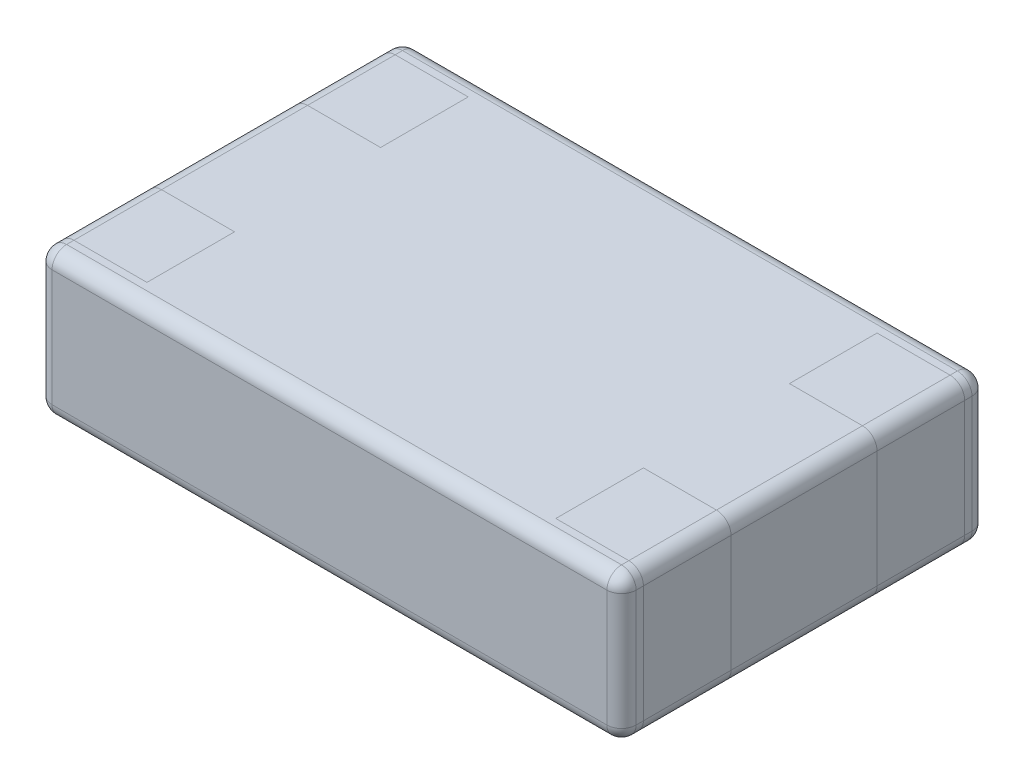
SolidWorks part; units mm, degrees
ref_plane "Front Plane" through (0, 0, 0) normal (0, 0, 1) x (1, 0, 0)
ref_plane "Top Plane" through (0, 0, 0) normal (0, 1, 0) x (1, 0, 0)
ref_plane "Right Plane" through (0, 0, 0) normal (1, 0, 0) x (0, 0, -1)
sketch "Sketch1" plane through (0, 0, 0) normal (0, 1, 0) x (1, 0, 0)
  line L0 (-1, -0.625) -> (1, 0.625) construction
  line L1 (-1, 0.625) -> (1, 0.625)
  line L2 (-1, 0.625) -> (-1, -0.625)
  line L3 (-1, -0.625) -> (1, -0.625)
  line L4 (1, 0.625) -> (1, -0.625)
  dimension "D1" = 2
  dimension "D2" = 1.25
extrude "Boss-Extrude1" add sketch "Sketch1" along normal blind 0.5
sketch "Sketch2" plane through (1, 0, 0) normal (1, 0, 0) x (0, 0, -1)
  line L0 (-0.625, 0) -> (0.625, 0) construction
  line L1 (-0.55, 0.5) -> (-0.25, 0.5)
  line L2 (-0.55, 0.5) -> (-0.55, 0)
  line L3 (-0.55, 0) -> (-0.25, 0)
  line L4 (-0.25, 0.5) -> (-0.25, 0)
  line L5 (-0.625, 0.5) -> (0.625, 0.5) construction
  line L6 (0.25, 0.5) -> (0.55, 0.5)
  line L7 (0.25, 0.5) -> (0.25, 0)
  line L8 (0.25, 0) -> (0.55, 0)
  line L9 (0.55, 0.5) -> (0.55, 0)
  line L10 (0.4, 0.5) -> (0.4, 0.5626) construction
  line L11 (-0.4, 0.5) -> (-0.4, 0.5626) construction
  line L12 (0, 0) -> (0, 0.1122) construction
  dimension "D1" = 0.8
  dimension "D2" = 0.3
sketch "Sketch3" plane through (-1, 0, 0) normal (-1, 0, 0) x (0, 0, 1)
  line L1 (0.25, 0.5) -> (0.55, 0.5)
  line L2 (0.25, 0.5) -> (0.25, 0)
  line L3 (0.25, 0) -> (0.55, 0)
  line L4 (0.55, 0.5) -> (0.55, 0)
  line L5 (-0.55, 0.5) -> (-0.25, 0.5)
  line L6 (-0.55, 0.5) -> (-0.55, 0)
  line L7 (-0.55, 0) -> (-0.25, 0)
  line L8 (-0.25, 0.5) -> (-0.25, 0)
split line "Split Line1"
split line "Split Line2"
sketch "Sketch4" plane through (0, 0.5, 0) normal (0, 1, 0) x (1, 0, 0)
  line L0 (0, 0) -> (0.2325, 0) construction
  line L1 (1, 0.25) -> (0.7, 0.25)
  line L2 (1, 0.25) -> (1, 0.55)
  line L3 (1, 0.55) -> (0.7, 0.55)
  line L4 (0.7, 0.25) -> (0.7, 0.55)
  line L5 (1, -0.25) -> (0.7, -0.25)
  line L6 (1, -0.25) -> (1, -0.55)
  line L7 (1, -0.55) -> (0.7, -0.55)
  line L8 (0.7, -0.25) -> (0.7, -0.55)
  line L9 (-1, -0.55) -> (-0.7, -0.55)
  line L10 (-1, -0.55) -> (-1, -0.25)
  line L11 (-1, -0.25) -> (-0.7, -0.25)
  line L12 (-0.7, -0.55) -> (-0.7, -0.25)
  line L13 (-1, 0.25) -> (-0.7, 0.25)
  line L14 (-1, 0.25) -> (-1, 0.55)
  line L15 (-1, 0.55) -> (-0.7, 0.55)
  line L16 (-0.7, 0.25) -> (-0.7, 0.55)
  line L17 (0.7, 0.4) -> (0.4751, 0.4) construction
  line L18 (0.7, -0.4) -> (0.5696, -0.4) construction
  dimension "D1" = 0.3
  dimension "D2" = 0.8
split line "Split Line3"
fillet "Fillet1" radius 0.05 28 edges at (-1, 0, -0.5875) (1, 0, 0.5875) (1, 0, -0.5875) (1, 0, -0.4) (1, 0, 0) (1, 0, 0.4) (1, 0.5, -0.4) (1, 0.5, 0.4) (1, 0.5, 0.5875) (1, 0.5, 0) (1, 0.5, -0.5875) (-1, 0, 0.5875) (-1, 0, 0.4) (-1, 0, 0) (-1, 0, -0.4) (-1, 0.5, 0.4) (-1, 0.5, -0.4) (-1, 0.5, 0) (-1, 0.5, 0.5875) (-1, 0.5, -0.5875) (1, 0.25, -0.625) (-1, 0.25, -0.625) (0, 0, -0.625) (-1, 0.25, 0.625) (1, 0.25, 0.625) (0, 0, 0.625) (0, 0.5, -0.625) (0, 0.5, 0.625)
